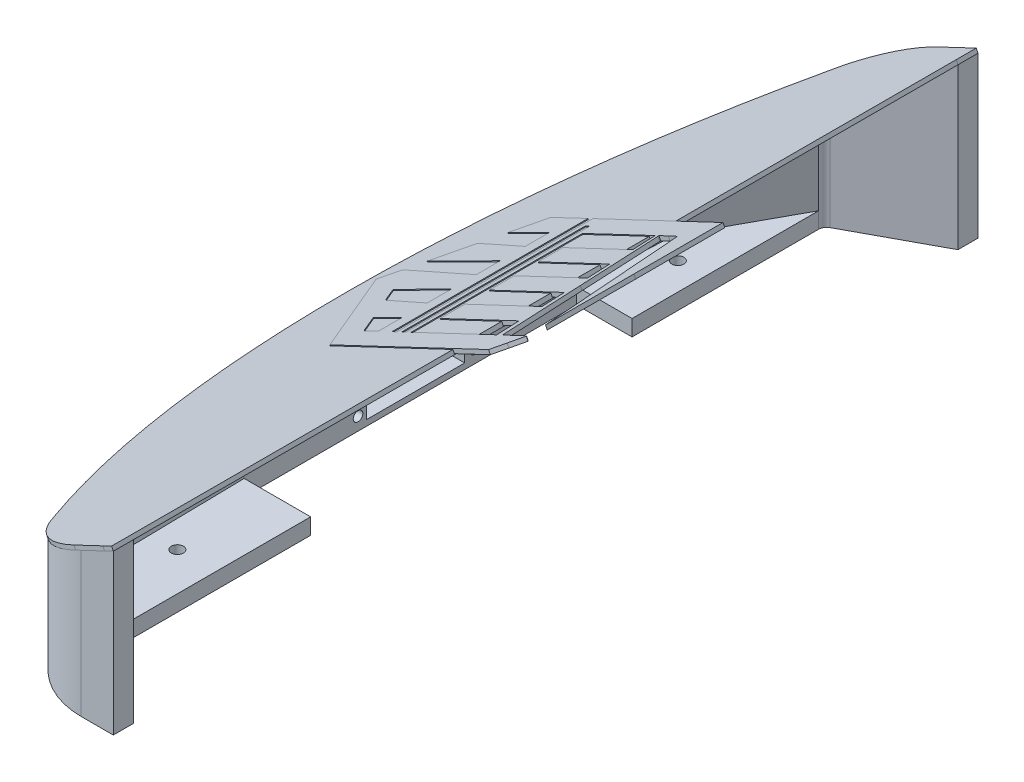
SolidWorks part; units mm, degrees
ref_plane "Front Plane" through (0, 0, 0) normal (0, 0, 1) x (1, 0, 0)
ref_plane "Top Plane" through (0, 0, 0) normal (0, 1, 0) x (1, 0, 0)
ref_plane "Right Plane" through (0, 0, 0) normal (1, 0, 0) x (0, 0, -1)
sketch "front_sketch" plane through (0, 0, 0) normal (0, 1, 0) x (1, 0, 0)
  line L4 (-94.9614, 124.4785) -> (-121.3453, 110.2345)
  line L10 (-122.6787, 107.9994) -> (-122.6787, 48.8108)
  line L24 (-94.9614, 130.8285) -> (-94.9614, 124.4785) construction
  line L25 (-94.9614, 124.4785) -> (-69.5614, 124.4785) construction
  line L28 (-95.6016, -142.8102) -> (-95.6016, -136.4602)
  line L29 (-95.6016, -136.4602) -> (-70.2016, -136.4602) construction
  line L34 (-122.6787, 48.8108) -> (-140.2508, 48.8108)
  line L36 (-140.2508, 48.8108) -> (-140.2508, -56.6452)
  line L43 (-140.2508, -56.6452) -> (-119.167, -56.6452)
  line L44 (-119.167, -56.6452) -> (-119.167, -126.1123)
  line L50 (-119.167, -126.1123) -> (-95.6016, -136.4602)
  line L129 (-94.9614, 130.8285) -> (-69.5614, 130.8285) construction
  line L130 (-94.9614, 130.8285) -> (-69.5614, 130.8285) construction
  line L225 (-95.5505, 130.8285) -> (-157.7358, 130.8285) construction
  line L248 (-94.9614, 130.8285) -> (-95.5505, 130.8285) construction
  line L254 (-94.9614, 130.8285) -> (-95.5505, 130.8285) construction
  line L257 (-94.9614, 130.8285) -> (-105.2412, 130.8285)
  line L258 (-95.5505, 130.8285) -> (-94.9614, 130.8285) construction
  line L259 (-95.6016, -142.8102) -> (-105.7982, -142.8102)
  line L260 (-94.9614, 124.4785) -> (-94.9614, 130.8285)
  line L261 (-94.9614, 130.8285) -> (-95.5505, 130.8285) construction
  line L263 (-95.6016, -142.8102) -> (-70.2016, -142.8102) construction
  line L264 (-95.6016, -142.8102) -> (-70.2016, -142.8102) construction
  line L267 (-97.1554, -142.8102) -> (-95.6016, -142.8102) construction
  line L294 (-94.9614, 130.8285) -> (-95.5505, 130.8285) construction
  line L295 (-157.7358, 130.8285) -> (-157.7358, -142.8102) construction
  line L296 (-157.7358, -142.8102) -> (-97.1554, -142.8102) construction
  line L297 (-95.5505, 130.8285) -> (-157.7358, 130.8285) construction
  arc A41 (-127.9188, 116.8691) -> (-128.5327, -128.7374) centre (116.7138, -6.5464) ccw
  arc A42 (-127.9188, 116.8691) -> (-105.2412, 130.8285) centre (-105.2412, 105.4285) cw
  arc A43 (-128.5327, -128.7374) -> (-105.7982, -142.8102) centre (-105.7982, -117.4102) ccw
  circle A44 centre (-131.2964, 71.9636) radius 1.905
  circle A45 centre (-131.2964, -86.7864) radius 1.905
  arc A48 (-122.6787, 107.9994) -> (-121.3453, 110.2345) centre (-120.1387, 107.9994) cw
  dimension "D12" = 25.4
  dimension "D14" = 25.4
  dimension "D30" = 3.81
  dimension "D4" = 2.54
  dimension "D19" = 6.35
  dimension "D27" = 10.2799
  dimension "D28" = 10.1966
extrude "Boss-Extrude1" add sketch "front_sketch" along normal blind 50.8
sketch "Sketch1" plane through (0, 50.8, 0) normal (0, 1, 0) x (1, 0, 0)
  line L0 (-122.6787, 48.8108) -> (-122.6787, 107.9994)
  line L1 (-122.6787, 107.9994) -> (-138.8333, 78.4051)
  line L2 (-138.8333, 78.4051) -> (-140.2508, 48.8108)
  line L3 (-140.2508, 48.8108) -> (-122.6787, 48.8108)
  line L4 (-119.167, -56.6452) -> (-140.2508, -56.6452)
  line L5 (-119.167, -56.6452) -> (-140.2508, -56.6452) construction
  line L6 (-140.2508, -56.6452) -> (-140.2508, 48.8108) construction
  line L7 (-140.2508, -56.6452) -> (-139.5421, -96.1925)
  line L8 (-139.5421, -96.1925) -> (-119.167, -126.1123)
  line L9 (-119.167, -126.1123) -> (-119.167, -56.6452) construction
  line L10 (-95.6016, -136.4602) -> (-119.167, -126.1123) construction
  line L11 (-119.167, -126.1123) -> (-119.167, -56.6452)
extrude "Cut-Extrude1" cut sketch "Sketch1" against normal blind 45.72
sketch "Sketch3" plane through (0, 0, 142.8102) normal (0, 0, 1) x (1, 0, 0)
  line L0 (-94.9614, 50.8) -> (-157.2871, 21.2708)
  line L1 (-157.2871, 50.8) -> (-157.2871, 0) construction
  line L2 (-157.2871, 21.2708) -> (-157.2871, 50.8)
  line L3 (-157.2871, 50.8) -> (-94.9614, 50.8)
extrude "Cut-Extrude2" cut sketch "Sketch3" against normal through all
sketch "Sketch4" plane through (-140.2508, 0, 0) normal (1, 0, 0) x (0, 0, -1)
  line L0 (-24.4046, 24.1445) -> (20.2563, 24.1445)
  line L1 (-24.4046, 24.1445) -> (-24.4046, 5.0945)
  line L3 (20.2563, 24.1445) -> (20.2563, 5.0945)
  line L4 (-24.4046, 5.0945) -> (-24.4046, 1.8437)
  line L5 (-24.4046, 1.8437) -> (20.2563, 1.8437)
  line L6 (20.2563, 1.8437) -> (20.2563, 5.0945)
  dimension "D1" = 19.05
extrude "Cut-Extrude3" cut sketch "Sketch4" against normal through all
sketch "Sketch6" plane through (-140.2508, 0, 0) normal (1, 0, 0) x (0, 0, -1)
  line L18 (-24.4046, 24.1445) -> (-24.4046, 1.8437) construction
  line L19 (-24.4046, 24.1445) -> (-17.8803, 24.1445)
  line L20 (-24.4046, 24.1445) -> (-24.4046, 1.8437)
  line L21 (-24.4046, 1.8437) -> (-17.8803, 1.8437)
  line L22 (-17.8803, 24.1445) -> (-17.8803, 1.8437)
  line L23 (-24.4046, 1.8437) -> (20.2563, 1.8437) construction
  line L24 (20.2563, 24.1445) -> (-24.4046, 24.1445) construction
  line L25 (20.2563, 1.8437) -> (13.2935, 1.8437)
  line L26 (20.2563, 1.8437) -> (20.2563, 24.1445)
  line L27 (20.2563, 24.1445) -> (13.2935, 24.1445)
  line L28 (13.2935, 1.8437) -> (13.2935, 24.1445)
  circle A1 centre (16.554, 4.1015) radius 1.524
  circle A2 centre (-20.53, 4.1015) radius 1.524
extrude "Boss-Extrude2" add sketch "Sketch6" against normal blind 10.16
sketch "Sketch8" plane through (-37.0648, 78.2307, 0) normal (-0.4282, 0.9037, 0) x (0.9037, 0.4282, 0)
  line L2 (-67.1537, 130.8054) -> (-64.066, 130.8285)
  line L3 (-64.066, 130.8285) -> (-64.066, 124.4785)
  line L5 (-64.066, 124.4785) -> (-64.7745, -142.8102)
  line L11 (-67.1537, 130.8054) -> (-41.7537, 130.8054) construction
  line L12 (-67.1537, 130.8054) -> (-41.7537, 130.8054) construction
  line L13 (-67.7427, 130.8054) -> (-129.9281, 130.8054) construction
  line L14 (-67.1537, 130.8054) -> (-67.7427, 130.8054) construction
  line L15 (-67.1537, 130.8054) -> (-67.7427, 130.8054) construction
  line L16 (-67.1537, 130.8054) -> (-77.4335, 130.8054)
  line L17 (-67.7427, 130.8054) -> (-67.1537, 130.8054) construction
  line L18 (-67.7939, -142.8333) -> (-77.9905, -142.8333)
  line L20 (-67.1537, 130.8054) -> (-67.7427, 130.8054) construction
  line L21 (-67.7939, -142.8333) -> (-42.3939, -142.8333) construction
  line L22 (-67.7939, -142.8333) -> (-42.3939, -142.8333) construction
  line L23 (-69.3477, -142.8333) -> (-67.7939, -142.8333) construction
  line L24 (-67.1537, 130.8054) -> (-67.7427, 130.8054) construction
  line L25 (-64.7745, -142.8102) -> (-67.7939, -142.8333)
  line L26 (-129.9281, -142.8333) -> (-69.3477, -142.8333) construction
  line L27 (-67.7427, 130.8054) -> (-129.9281, 130.8054) construction
  arc A1 (-100.1111, 116.8461) -> (-77.4335, 130.8054) centre (-77.4335, 105.4054) cw
  arc A2 (-100.725, -128.7605) -> (-77.9905, -142.8333) centre (-77.9905, -117.4333) ccw
  arc A6 (-100.1111, 116.8461) -> (-100.725, -128.7605) centre (113.7895, -6.4926) ccw
  dimension "D1" = 25.4
  dimension "D2" = 25.4
  dimension "D3" = 10.2799
  dimension "D4" = 10.1966
sketch "logo" plane through (-37.1736, 78.4603, 0) normal (-0.4282, 0.9037, 0) x (0.9037, 0.4282, 0)
  line L0 (-72.6596, -26.9928) -> (-57.6338, -26.9928)
  line L1 (-57.6338, -26.9928) -> (-57.6755, -26.6856)
  line L2 (-58.2482, -19.8316) -> (-58.3051, -19.3353)
  line L3 (-58.3051, -19.3353) -> (-72.1443, -19.3353)
  line L4 (-72.1443, -19.3353) -> (-85.9834, -19.3353)
  line L5 (-85.9834, -19.3353) -> (-85.9834, -15.4119)
  line L6 (-85.9834, -15.4119) -> (-85.9834, -11.4885)
  line L7 (-85.9834, -11.4885) -> (-72.4643, -11.4885)
  line L8 (-72.4643, -11.4885) -> (-58.9451, -11.4885)
  line L9 (-58.9451, -11.4885) -> (-58.9517, -11.1813)
  line L10 (-59.259, -7.3288) -> (-59.5595, -3.7836)
  line L11 (-59.5595, -3.7836) -> (-72.7713, -3.7617)
  line L12 (-72.7713, -3.7617) -> (-85.9832, -3.7397)
  line L13 (-85.9832, -3.7397) -> (-85.9832, 0.1833)
  line L14 (-85.9832, 0.1833) -> (-85.9832, 4.1064)
  line L15 (-85.9832, 4.1064) -> (-73.0809, 4.1064)
  line L16 (-73.0809, 4.1064) -> (-60.178, 4.1064)
  line L17 (-60.178, 4.1064) -> (-60.2253, 4.5081)
  line L18 (-60.7956, 11.3622) -> (-60.8478, 11.7639)
  line L19 (-60.8478, 11.7639) -> (-73.4158, 11.7639)
  line L20 (-73.4158, 11.7639) -> (-85.9837, 11.7639)
  line L21 (-85.9837, 11.7639) -> (-85.9837, 15.6873)
  line L22 (-85.9837, 15.6873) -> (-85.9837, 19.6106)
  line L23 (-85.9837, 19.6106) -> (-73.7409, 19.6106)
  line L24 (-73.7409, 19.6106) -> (-61.498, 19.6106)
  line L25 (-61.498, 19.6106) -> (-61.498, 19.8503)
  line L26 (-87.6854, 0.1195) -> (-87.6854, -26.9974)
  line L27 (-87.6854, -26.9974) -> (-72.6596, -26.9928)
  line L28 (-90.1907, -26.9928) -> (-89.3871, -26.9928)
  line L29 (-89.3871, -26.9928) -> (-89.3871, 2.078)
  line L30 (-89.3871, 2.078) -> (-89.3871, 31.1489)
  line L31 (-89.3871, 31.1489) -> (-90.1907, 31.1489)
  line L32 (-90.1907, 31.1489) -> (-90.9942, 31.1489)
  line L33 (-90.9942, 31.1489) -> (-90.9942, 2.078)
  line L34 (-90.9942, 2.078) -> (-90.9942, -26.9928)
  line L35 (-90.9942, -26.9928) -> (-90.1907, -26.9928)
  line L36 (-106.3816, -23.6839) -> (-104.272, -26.9455)
  line L37 (-104.272, -26.9455) -> (-101.7456, -26.973)
  line L38 (-101.7456, -26.973) -> (-99.2192, -27.0005)
  line L39 (-99.2192, -27.0005) -> (-99.2192, -23.1701)
  line L40 (-99.2192, -23.1701) -> (-99.2192, -19.3397)
  line L41 (-99.2192, -19.3397) -> (-99.4682, -19.3397)
  line L42 (-108.1754, -19.8661) -> (-108.7649, -19.9216)
  line L43 (-108.7649, -19.9216) -> (-108.628, -20.1744)
  line L44 (-106.3816, -23.6887) -> (-106.3816, -23.6839)
  line L45 (-116.331, -8.2104) -> (-114.7715, -10.6297)
  line L46 (-114.7715, -10.6297) -> (-114.2985, -10.6792)
  line L47 (-99.7628, -11.4447) -> (-99.2191, -11.4997)
  line L48 (-99.2191, -11.4997) -> (-99.2191, -7.6131)
  line L49 (-99.2191, -7.6131) -> (-99.2191, -3.7265)
  line L50 (-99.2191, -3.7265) -> (-99.6209, -3.7759)
  line L51 (-99.6682, 4.1153) -> (-99.2192, 4.1105)
  line L52 (-99.2192, 4.1105) -> (-99.2192, 7.9393)
  line L53 (-100.0464, 19.6657) -> (-99.2192, 19.608)
  line L54 (-99.2192, 19.608) -> (-99.2192, 23.4758)
  line L55 (-99.2192, 23.4758) -> (-99.2192, 27.3437)
  line L56 (-99.2192, 27.3437) -> (-99.621, 27.3053)
  line L57 (-100.9093, 35.2121) -> (-94.3977, 35.2121)
  line L58 (-94.3977, 35.2121) -> (-94.3977, 4.1087)
  line L59 (-94.3977, 4.1087) -> (-94.3977, -26.9948)
  line L60 (-94.3977, -26.9948) -> (-93.5468, -26.9948)
  line L61 (-93.5468, -26.9948) -> (-92.6959, -26.9948)
  line L62 (-92.6959, -26.9948) -> (-92.6959, 4.1087)
  line L63 (-92.6959, 4.1087) -> (-92.6959, 35.2121)
  line L64 (-92.6959, 35.2121) -> (-69.8647, 35.2121)
  line L65 (-69.8647, 35.2121) -> (-47.0335, 35.2121)
  line L66 (-47.0335, 35.2121) -> (-47.0461, 6.9684)
  line L67 (-57.5351, 27.3654) -> (-60.8523, 27.3654)
  line L68 (-60.8523, 27.3654) -> (-60.7985, 27.011)
  line L69 (-55.6775, -26.7819) -> (-55.6325, -26.9946)
  line L70 (-55.6325, -26.9946) -> (-51.3327, -26.9946)
  line L71 (-49.4296, -31.0713) -> (-51.8262, -34.7941)
  line L72 (-51.8262, -34.7941) -> (-79.6679, -34.8161)
  line L73 (-79.6679, -34.8161) -> (-107.5096, -34.8381)
  line L74 (-107.5096, -34.8381) -> (-118.6499, -17.5135)
  line L75 (-128.3681, 2.7416) -> (-128.3686, 2.7398)
  spline S0 degree 3 poles (-57.6755, -26.6856) (-57.6986, -26.5169) (-57.8241, -25.017) (-57.9544, -23.3531) knots 0 0 0 0 1 1 1 1
  spline S1 degree 3 poles (-57.9544, -23.3531) (-58.0847, -21.6892) (-58.2169, -20.1046) (-58.2482, -19.8316) knots 0 0 0 0 1 1 1 1
  spline S2 degree 3 poles (-58.9517, -11.1813) (-58.9554, -11.0121) (-59.0937, -9.2787) (-59.259, -7.3288) knots 0 0 0 0 1 1 1 1
  spline S3 degree 3 poles (-60.2253, 4.5081) (-60.2511, 4.729) (-60.3784, 6.2713) (-60.5078, 7.9352) knots 0 0 0 0 1 1 1 1
  spline S4 degree 3 poles (-60.5078, 7.9352) (-60.6374, 9.5991) (-60.7669, 11.1412) (-60.7956, 11.3622) knots 0 0 0 0 1 1 1 1
  spline S5 degree 3 poles (-61.498, 19.8503) (-61.498, 20.2509) (-62.0691, 27.118) (-62.1129, 27.2446) knots 0 0 0 0 1 1 1 1
  spline S6 degree 3 poles (-62.1129, 27.2446) (-62.1454, 27.3386) (-64.7793, 27.3628) (-74.8566, 27.3628) knots 0 0 0 0 1 1 1 1
  spline S7 degree 3 poles (-74.8566, 27.3628) (-81.8431, 27.3628) (-87.5877, 27.3353) (-87.6224, 27.2996) knots 0 0 0 0 1 1 1 1
  spline S8 degree 3 poles (-87.6224, 27.2996) (-87.657, 27.2666) (-87.6854, 15.0339) (-87.6854, 0.1195) knots 0 0 0 0 1 1 1 1
  spline S9 degree 3 poles (-99.4682, -19.3397) (-99.8479, -19.3397) (-107.5038, -19.8024) (-108.1754, -19.8661) knots 0 0 0 0 1 1 1 1
  spline S10 degree 3 poles (-108.628, -20.1744) (-108.5527, -20.3135) (-107.5419, -21.8948) (-106.3816, -23.6887) knots 0 0 0 0 1 1 1 1
  spline S11 degree 3 poles (-114.2985, -10.6792) (-114.0383, -10.7067) (-110.7837, -10.8781) (-107.0659, -11.0606) knots 0 0 0 0 1 1 1 1
  spline S12 degree 3 poles (-107.0659, -11.0606) (-103.3482, -11.243) (-100.0617, -11.4161) (-99.7628, -11.4447) knots 0 0 0 0 1 1 1 1
  spline S13 degree 3 poles (-99.6209, -3.7759) (-99.8419, -3.8034) (-104.1068, -4.0667) (-109.0985, -4.3589) knots 0 0 0 0 1 1 1 1
  spline S14 degree 3 poles (-109.0985, -4.3589) (-114.0902, -4.6512) (-118.2282, -4.9056) (-118.2941, -4.9252) knots 0 0 0 0 1 1 1 1
  spline S15 degree 3 poles (-118.2941, -4.9252) (-118.4312, -4.9636) (-118.5325, -4.7955) (-116.331, -8.2104) knots 0 0 0 0 1 1 1 1
  spline S16 degree 3 poles (-128.3686, 2.7398) (-127.4625, 4.1437) (-126.67, 5.3388) (-126.6075, 5.3957) knots 0 0 0 0 1 1 1 1
  spline S17 degree 3 poles (-126.6075, 5.3957) (-126.5249, 5.4704) (-122.878, 5.31) (-113.3055, 4.8095) knots 0 0 0 0 1 1 1 1
  spline S18 degree 3 poles (-113.3055, 4.8095) (-106.052, 4.4304) (-99.9152, 4.1179) (-99.6682, 4.1153) knots 0 0 0 0 1 1 1 1
  spline S19 degree 3 poles (-99.2192, 7.9393) (-99.2192, 10.0451) (-99.2511, 11.7692) (-99.2901, 11.7706) knots 0 0 0 0 1 1 1 1
  spline S20 degree 3 poles (-99.2901, 11.7706) (-99.3291, 11.7706) (-104.754, 11.4463) (-111.3454, 11.0473) knots 0 0 0 0 1 1 1 1
  spline S21 degree 3 poles (-111.3454, 11.0473) (-117.9368, 10.6483) (-123.3508, 10.3427) (-123.3766, 10.3684) knots 0 0 0 0 1 1 1 1
  spline S22 degree 3 poles (-123.3766, 10.3684) (-123.4211, 10.4124) (-117.1766, 20.2031) (-116.9561, 20.4345) knots 0 0 0 0 1 1 1 1
  spline S23 degree 3 poles (-116.9561, 20.4345) (-116.8758, 20.5186) (-114.9494, 20.4455) (-108.8622, 20.1339) knots 0 0 0 0 1 1 1 1
  spline S24 degree 3 poles (-108.8622, 20.1339) (-104.4685, 19.908) (-100.5014, 19.697) (-100.0464, 19.6657) knots 0 0 0 0 1 1 1 1
  spline S25 degree 3 poles (-99.621, 27.3053) (-100.7533, 27.2014) (-112.9477, 26.5035) (-112.9849, 26.5407) knots 0 0 0 0 1 1 1 1
  spline S26 degree 3 poles (-112.9849, 26.5407) (-113.0234, 26.5791) (-107.7997, 34.7558) (-107.5274, 35.084) knots 0 0 0 0 1 1 1 1
  spline S27 degree 3 poles (-107.5274, 35.084) (-107.4396, 35.1895) (-106.2764, 35.2121) (-100.9093, 35.2121) knots 0 0 0 0 1 1 1 1
  spline S28 degree 3 poles (-47.0461, 6.9684) (-47.0533, -8.5655) (-47.078, -21.1688) (-47.1005, -21.0388) knots 0 0 0 0 1 1 1 1
  spline S29 degree 3 poles (-47.1005, -21.0388) (-47.1776, -20.603) (-54.218, 27.1919) (-54.218, 27.2792) knots 0 0 0 0 1 1 1 1
  spline S30 degree 3 poles (-54.218, 27.2792) (-54.218, 27.3286) (-55.603, 27.3654) (-57.5351, 27.3654) knots 0 0 0 0 1 1 1 1
  spline S31 degree 3 poles (-60.7985, 27.011) (-60.7688, 26.8159) (-59.6147, 14.6806) (-58.2337, 0.0436) knots 0 0 0 0 1 1 1 1
  spline S32 degree 3 poles (-58.2337, 0.0436) (-56.8526, -14.5934) (-55.7023, -26.6649) (-55.6775, -26.7819) knots 0 0 0 0 1 1 1 1
  spline S33 degree 3 poles (-51.3327, -26.9946) (-47.1947, -26.9946) (-47.033, -27.0001) (-47.033, -27.1715) knots 0 0 0 0 1 1 1 1
  spline S34 degree 3 poles (-47.033, -27.1715) (-47.033, -27.2688) (-48.1115, -29.0237) (-49.4296, -31.0713) knots 0 0 0 0 1 1 1 1
  spline S35 degree 3 poles (-118.6499, -17.5135) (-124.777, -7.9851) (-129.8408, -0.104) (-129.9028, 0) knots 0 0 0 0 1 1 1 1
  spline S36 degree 3 poles (-129.9028, 0) (-130.0023, 0.1671) (-129.8234, 0.4869) (-128.3681, 2.7416) knots 0 0 0 0 1 1 1 1
sketch "Sketch9" plane through (-150.4108, 0, 0) normal (-1, 0, 0) x (0, 0, 1)
  line L0 (-20.2563, 1.8437) -> (-20.2563, 24.1445) construction
  line L1 (-20.2563, 9.171) -> (-13.2935, 9.171)
  line L2 (-20.2563, 9.171) -> (-20.2563, 1.8437)
  line L3 (-20.2563, 1.8437) -> (-13.2935, 1.8437)
  line L4 (-13.2935, 9.171) -> (-13.2935, 1.8437)
  line L5 (24.4046, 21.5468) -> (24.4046, 1.8437) construction
  line L6 (17.8803, 1.8437) -> (24.4046, 1.8437)
  line L7 (17.8803, 1.8437) -> (17.8803, 9.171)
  line L8 (17.8803, 9.171) -> (24.4046, 9.171)
  line L9 (24.4046, 1.8437) -> (24.4046, 9.171)
extrude "Boss-Extrude3" add sketch "Sketch9" along normal blind 7.62
sketch "Sketch10" plane through (-158.0308, 0, 0) normal (-1, 0, 0) x (0, 0, 1)
  circle A0 centre (-16.554, 4.1015) radius 1.524
  circle A1 centre (20.53, 4.1015) radius 1.524
extrude "Cut-Extrude4" cut sketch "Sketch10" against normal through all
extrude "Boss-Extrude5" add sketch "Sketch8" along normal blind 1.27
extrude "Boss-Extrude6" add sketch "logo" along normal blind 1.27
